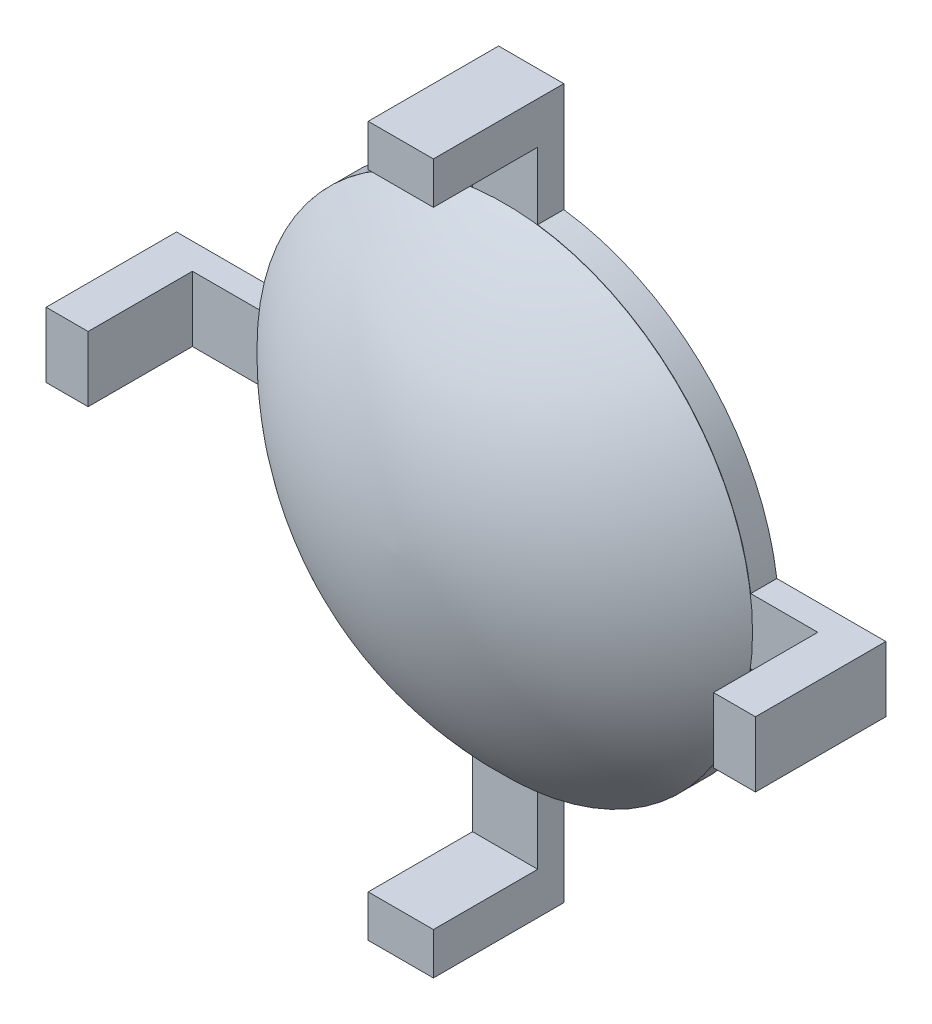
SolidWorks part; units mm, degrees
ref_plane "Front Plane" through (0, 0, 0) normal (0, 0, 1) x (1, 0, 0)
ref_plane "Top Plane" through (0, 0, 0) normal (0, 1, 0) x (1, 0, 0)
ref_plane "Right Plane" through (0, 0, 0) normal (1, 0, 0) x (0, 0, -1)
sketch "Sketch1" plane through (0, 0, 0) normal (0, 0, 1) x (1, 0, 0)
  line L0 (0, -55) -> (0, 55) construction
  line L1 (-13.6, -1.25) -> (13.6, -1.25)
  line L2 (-13.6, -1.25) -> (-13.6, 1.25)
  line L3 (-13.6, 1.25) -> (13.6, 1.25)
  line L4 (13.6, -1.25) -> (13.6, 1.25)
  line L5 (-13.6, -1.25) -> (13.6, 1.25) construction
  line L6 (-13.6, 1.25) -> (13.6, -1.25) construction
  line L7 (-1.25, 13.6) -> (1.25, 13.6)
  line L8 (-1.25, 13.6) -> (-1.25, -13.6)
  line L9 (-1.25, -13.6) -> (1.25, -13.6)
  line L10 (1.25, 13.6) -> (1.25, -13.6)
  line L11 (13.6, 1.25) -> (13.6, -1.25)
  line L12 (13.6, 1.25) -> (-13.6, 1.25)
  line L13 (-13.6, 1.25) -> (-13.6, -1.25)
  line L14 (13.6, -1.25) -> (-13.6, -1.25)
  line L15 (1.25, -13.6) -> (-1.25, -13.6)
  line L16 (1.25, -13.6) -> (1.25, 13.6)
  line L17 (1.25, 13.6) -> (-1.25, 13.6)
  line L18 (-1.25, -13.6) -> (-1.25, 13.6)
  line L19 (55, 0) -> (-55, 0) construction
  circle A0 centre (0, 0) radius 9.5
  point P22 (0, 0)
  dimension "D1" = 27.2
  dimension "D2" = 19
  dimension "D3" = 0
  dimension "D4" = 2.5
  dimension "D5" = 4
extrude "Boss-Extrude1" add sketch "Sketch1" along normal blind 1 contours A0 L3 L2 L1 | A0 L14 L4 L12 | L15 L18 L17 L16
sketch "Sketch2" plane through (0, 0, 1) normal (0, 0, 1) x (1, 0, 0)
  line L0 (-13.6, 1.25) -> (-9.4174, 1.25) construction
  line L1 (-13.6, 1.25) -> (-11.9906, 1.25)
  line L2 (-13.6, 1.25) -> (-13.6, -1.25)
  line L3 (-13.6, -1.25) -> (-11.9906, -1.25)
  line L4 (-11.9906, 1.25) -> (-11.9906, -1.25)
  line L5 (1.25, 13.6) -> (-1.25, 13.6)
  line L6 (1.25, 13.6) -> (1.25, 11.9906)
  line L7 (1.25, 11.9906) -> (-1.25, 11.9906)
  line L8 (-1.25, 13.6) -> (-1.25, 11.9906)
  line L9 (13.6, -1.25) -> (13.6, 1.25)
  line L10 (13.6, -1.25) -> (11.9906, -1.25)
  line L11 (11.9906, -1.25) -> (11.9906, 1.25)
  line L12 (13.6, 1.25) -> (11.9906, 1.25)
  line L13 (-1.25, -13.6) -> (1.25, -13.6)
  line L14 (-1.25, -13.6) -> (-1.25, -11.9906)
  line L15 (-1.25, -11.9906) -> (1.25, -11.9906)
  line L16 (1.25, -13.6) -> (1.25, -11.9906)
  point P21 (0, 0)
  dimension "D1" = 2.5
  dimension "D2" = 0
  dimension "D3" = 4
extrude "Boss-Extrude2" add sketch "Sketch2" along normal blind 4
sketch "Sketch7" plane through (0, 0, 0) normal (0, 1, 0) x (1, 0, 0)
  line L0 (-0.0002, -0.0119) -> (-0.0002, -1.0119)
  line L1 (-0.0002, -1.0119) -> (-9.5002, -1.0119)
  line L2 (-0.0002, -1.0119) -> (-0.0002, -5.2119)
  line L3 (-0.0002, -5.2119) -> (-0.0002, -6.238) construction
  arc A0 (-9.5002, -1.0119) -> (-0.0002, -5.2119) centre (0.3213, 8.3592) ccw
  dimension "D1" = 1
  dimension "D2" = 9.5
revolve "Revolve4" add sketch "Sketch7" angle 360 about L3
